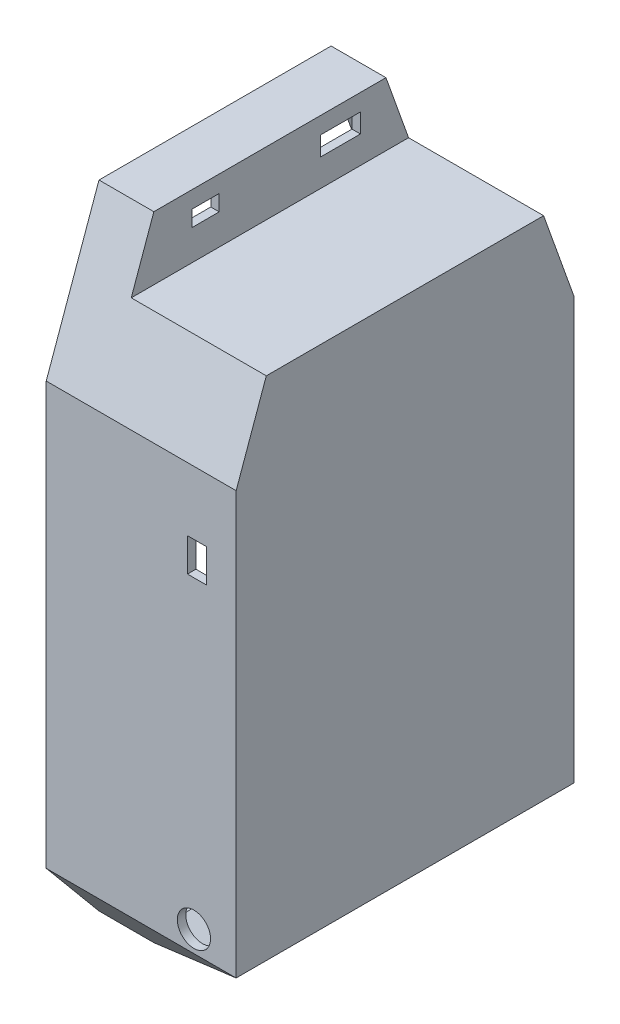
SolidWorks part; units mm, degrees
material "Balsa"
ref_plane "Front Plane" through (0, 0, 0) normal (0, 0, 1) x (1, 0, 0)
ref_plane "Top Plane" through (0, 0, 0) normal (0, 1, 0) x (1, 0, 0)
ref_plane "Right Plane" through (0, 0, 0) normal (1, 0, 0) x (0, 0, -1)
sketch "Sketch1" plane through (0, 0, 0) normal (0, 0, 1) x (1, 0, 0)
  line L0 (0, 0) -> (0, 190.5)
  line L1 (0, 190.5) -> (16.51, 190.5)
  line L2 (57.15, 171.45) -> (57.15, 19.05)
  line L3 (16.51, 0) -> (0, 0)
  line L4 (57.15, 171.45) -> (16.51, 171.45)
  line L5 (57.15, 19.05) -> (16.51, 0)
  line L6 (0, 95.25) -> (57.15, 95.25) construction
  line L7 (16.51, 171.45) -> (16.51, 190.5)
  dimension "D3" = 57.15
  dimension "D1" = 190.5
  dimension "D2" = 152.4
  dimension "D4" = 40.64
extrude "Boss-Extrude2" add sketch "Sketch1" along normal blind 101.6 contours L7 L4 L2 L5 L3 L0 L1
sketch "Sketch2" plane through (0, 0, 0) normal (-1, 0, 0) x (0, 0, 1)
  line L0 (15.875, 190.5) -> (0, 146.05)
  line L1 (101.6, 190.5) -> (0, 190.5) construction
  line L2 (0, 0) -> (0, 190.5) construction
  line L3 (0, 146.05) -> (0, 19.05) construction
  line L4 (0, 19.05) -> (15.875, 0)
  line L5 (101.6, 0) -> (0, 0) construction
  line L6 (15.875, 0) -> (85.725, 0) construction
  line L7 (85.725, 0) -> (101.6, 19.05)
  line L8 (101.6, 0) -> (101.6, 190.5) construction
  line L9 (101.6, 146.05) -> (101.6, 19.05) construction
  line L10 (101.6, 146.05) -> (85.725, 190.5)
  line L11 (85.725, 190.5) -> (15.875, 190.5) construction
  line L12 (50.8, 190.5) -> (50.8, 0) construction
  line L13 (0, 95.25) -> (101.6, 95.25) construction
  line L14 (101.6, 0) -> (101.6, 190.5) construction
  line L15 (101.6, 190.5) -> (0, 190.5) construction
  line L16 (15.875, 190.5) -> (0, 190.5)
  line L17 (0, 190.5) -> (0, 146.05)
  line L18 (0, 19.05) -> (0, 0)
  line L19 (0, 0) -> (15.875, 0)
  line L20 (85.725, 0) -> (101.6, 0)
  line L21 (101.6, 0) -> (101.6, 19.05)
  line L22 (101.6, 146.05) -> (101.6, 190.5)
  line L23 (101.6, 190.5) -> (85.725, 190.5)
  dimension "D1" = 69.85
  dimension "D2" = 69.85
  dimension "D3" = 76.2
  dimension "D4" = 76.2
  dimension "D5" = 50.8
  dimension "D6" = 50.8
extrude "Cut-Extrude1" cut sketch "Sketch2" against normal through all
shell "Shell1" thickness 2.54
sketch "Sketch3" plane through (16.51, 0, 0) normal (1, 0, 0) x (0, 0, -1)
  line L0 (-50.8, 190.5) -> (-50.8, 0) construction
  line L1 (-74.2474, 185.42) -> (-66.0474, 185.42)
  line L2 (-74.2474, 185.42) -> (-74.2474, 180.62)
  line L3 (-74.2474, 180.62) -> (-66.0474, 180.62)
  line L4 (-66.0474, 185.42) -> (-66.0474, 180.62)
  line L5 (-23.56, 185.42) -> (-35.56, 185.42)
  line L6 (-23.56, 185.42) -> (-23.56, 179.67)
  line L7 (-23.56, 179.67) -> (-35.56, 179.67)
  line L8 (-35.56, 185.42) -> (-35.56, 179.67)
  line L9 (-85.725, 190.5) -> (-15.875, 190.5) construction
  line L10 (-85.725, 0) -> (-15.875, 0) construction
  line L11 (-66.0474, 183.02) -> (-50.8, 183.02) construction
  line L12 (-50.8, 183.02) -> (-35.56, 182.545) construction
  dimension "D1" = 8.2
  dimension "D2" = 4.8
  dimension "D3" = 12
  dimension "D4" = 5.75
  dimension "D5" = 5.08
  dimension "D6" = 15.24
extrude "Cut-Extrude2" cut sketch "Sketch3" against normal through all
sketch "Sketch4" plane through (0, 0, 101.6) normal (0, 0, 1) x (1, 0, 0)
  line L0 (57.15, 146.05) -> (57.15, 19.05) construction
  line L1 (42.51, 127) -> (48.26, 127)
  line L2 (42.51, 127) -> (42.51, 117)
  line L3 (42.51, 117) -> (48.26, 117)
  line L4 (48.26, 127) -> (48.26, 117)
  line L5 (57.15, 146.05) -> (0, 146.05) construction
  point P4 (48.26, 122)
  dimension "D1" = 8.89
  dimension "D2" = 5.75
  dimension "D3" = 10
  dimension "D4" = 19.05
extrude "Cut-Extrude3" cut sketch "Sketch4" against normal blind 27.94
sketch "Sketch5" plane through (0, 0, 0) normal (0, 0, -1) x (-1, 0, 0)
  line L2 (-48.26, 127) -> (-42.51, 127) construction
  line L4 (-48.26, 114.25) -> (-42.51, 114.25)
  line L5 (-48.26, 114.25) -> (-48.26, 127)
  line L6 (-48.26, 127) -> (-42.51, 127)
  line L7 (-42.51, 127) -> (-42.51, 114.25)
  line L8 (-57.15, 146.05) -> (-57.15, 19.05) construction
  dimension "D1" = 12.75
  dimension "D2" = 8.89
extrude "Cut-Extrude4" cut sketch "Sketch5" against normal blind 27.94
sketch "Sketch6" plane through (0, 0, 101.6) normal (0, 0, 1) x (1, 0, 0)
  line L0 (57.15, 19.05) -> (0, 19.05) construction
  line L2 (57.15, 146.05) -> (57.15, 19.05) construction
  circle A0 centre (44.45, 25.4) radius 5
  dimension "D1" = 10
  dimension "D2" = 6.35
  dimension "D3" = 12.7
extrude "Cut-Extrude5" cut sketch "Sketch6" against normal blind 27.94
sketch "Sketch7" plane through (54.61, 0, 0) normal (-1, 0, 0) x (0, 0, 1)
  line L6 (99.06, 145.61) -> (90.7386, 168.91)
  line L7 (90.7386, 168.91) -> (10.8614, 168.91)
  line L8 (10.8614, 168.91) -> (2.54, 145.61)
  line L9 (2.54, 145.61) -> (2.54, 20.6646)
  line L10 (2.54, 20.6646) -> (99.06, 20.6646)
  line L11 (99.06, 20.6646) -> (99.06, 145.61)
  line L12 (99.06, 145.61) -> (90.7386, 168.91) construction
  line L13 (90.7386, 168.91) -> (10.8614, 168.91) construction
  line L14 (10.8614, 168.91) -> (2.54, 145.61) construction
  line L15 (2.54, 145.61) -> (2.54, 20.6646) construction
  line L16 (2.54, 20.6646) -> (99.06, 20.6646) construction
  line L17 (99.06, 20.6646) -> (99.06, 145.61) construction
  dimension "D1" = 0
